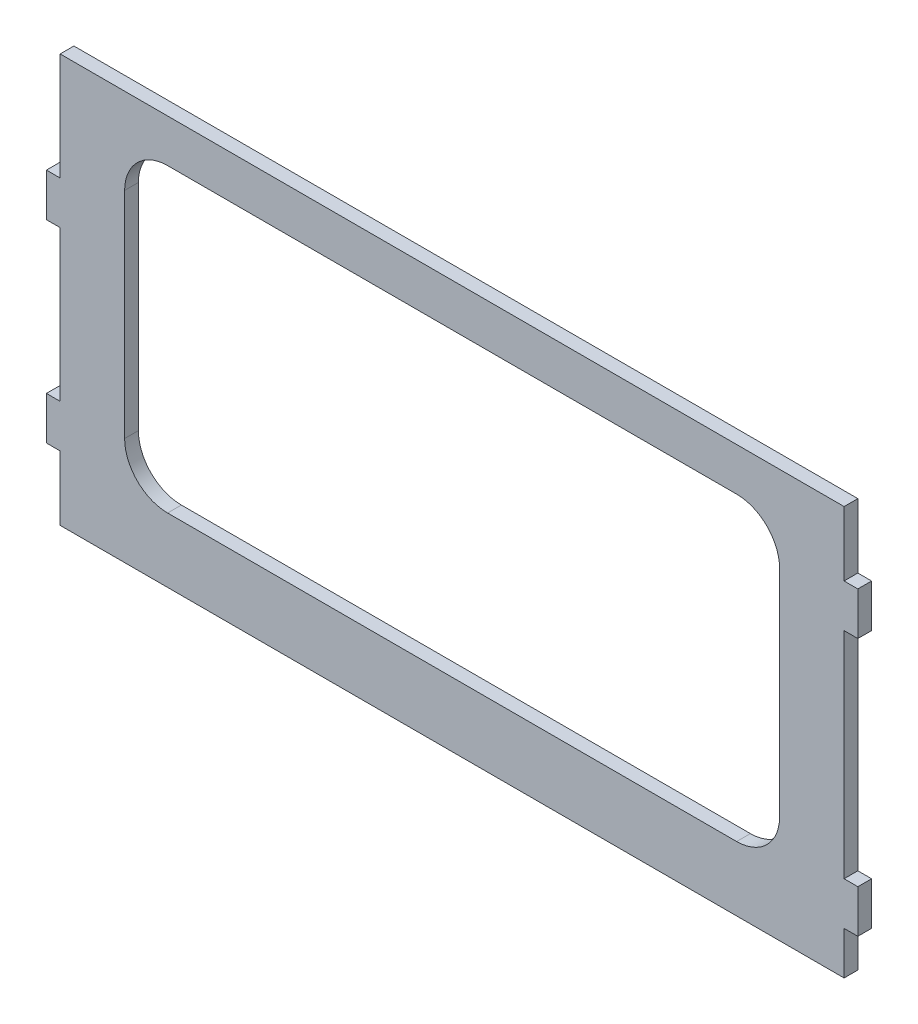
SolidWorks part; units mm, degrees
ref_plane "Front Plane" through (0, 0, 0) normal (0, 0, 1) x (1, 0, 0)
ref_plane "Top Plane" through (0, 0, 0) normal (0, 1, 0) x (1, 0, 0)
ref_plane "Right Plane" through (0, 0, 0) normal (1, 0, 0) x (0, 0, -1)
sketch "Sketch1" plane through (0, 0, 0) normal (0, 0, 1) x (1, 0, 0)
  line L1 (129.8145, -95.25) -> (125.7505, -95.25) construction
  line L2 (125.7505, 0) -> (-105.8975, 0)
  line L3 (125.7505, 0) -> (125.7505, -19.05)
  line L4 (125.7505, -120.65) -> (-105.8975, -120.65)
  line L6 (-105.8975, 0) -> (-105.8975, -31.75)
  line L7 (125.7505, -19.05) -> (129.8145, -19.05)
  line L8 (125.7505, 0) -> (-105.8975, 0) construction
  line L9 (125.7505, -31.75) -> (129.8145, -31.75)
  line L10 (129.8145, -19.05) -> (129.8145, -31.75)
  line L11 (129.8145, -107.95) -> (125.7505, -107.95)
  line L12 (129.8145, -107.95) -> (129.8145, -95.25)
  line L13 (129.8145, -95.25) -> (125.7505, -95.25)
  line L14 (125.7505, -31.75) -> (125.7505, -95.25)
  line L15 (-105.8975, -44.45) -> (-105.8975, -88.9)
  line L16 (-109.9615, -31.75) -> (-105.8975, -31.75)
  line L17 (-109.9615, -31.75) -> (-109.9615, -44.45)
  line L18 (-109.9615, -44.45) -> (-105.8975, -44.45)
  line L19 (-105.8975, -101.6) -> (-105.8975, -120.65)
  line L20 (-109.9615, -88.9) -> (-105.8975, -88.9)
  line L21 (-109.9615, -88.9) -> (-109.9615, -101.6)
  line L22 (-109.9615, -101.6) -> (-105.8975, -101.6)
  line L23 (125.7505, -107.95) -> (125.7505, -120.65)
extrude "Boss-Extrude1" add sketch "Sketch1" along normal blind 4.064
sketch "Sketch2" plane through (0, 0, 4.064) normal (0, 0, 1) x (1, 0, 0)
  line L0 (-105.8975, -120.65) -> (125.7505, -120.65) construction
  line L1 (-74.1475, -12.7) -> (94.0005, -12.7)
  line L2 (-86.8475, -25.4) -> (-86.8475, -88.9)
  line L3 (-74.1475, -101.6) -> (94.0005, -101.6)
  line L4 (106.7005, -25.4) -> (106.7005, -88.9)
  line L5 (125.7505, 0) -> (-105.8975, 0) construction
  line L6 (-105.8975, -44.45) -> (-105.8975, -88.9) construction
  line L7 (125.7505, -95.25) -> (125.7505, -31.75) construction
  arc A0 (94.0005, -101.6) -> (106.7005, -88.9) centre (94.0005, -88.9) ccw
  arc A1 (94.0005, -12.7) -> (106.7005, -25.4) centre (94.0005, -25.4) cw
  arc A2 (-74.1475, -12.7) -> (-86.8475, -25.4) centre (-74.1475, -25.4) ccw
  arc A3 (-86.8475, -88.9) -> (-74.1475, -101.6) centre (-74.1475, -88.9) ccw
  dimension "D5" = 12.7
  dimension "D1" = 19.05
  dimension "D2" = 12.7
  dimension "D3" = 19.05
  dimension "D4" = 19.05
extrude "Cut-Extrude1" cut sketch "Sketch2" against normal through all
